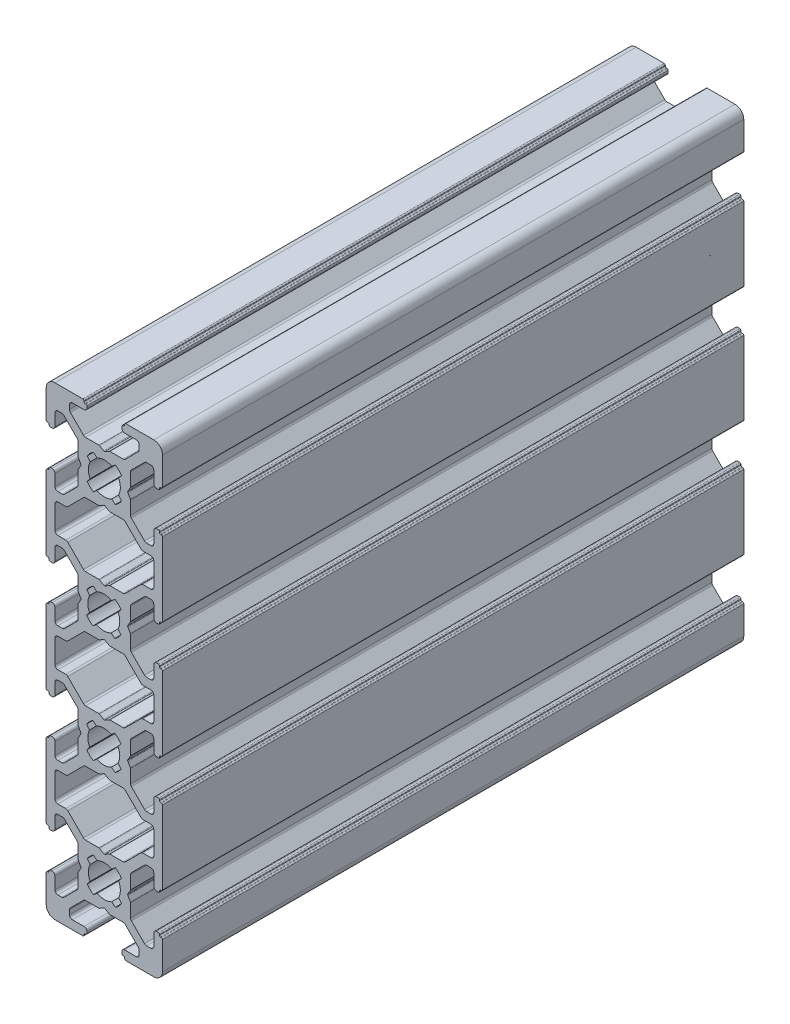
SolidWorks part; units mm, degrees
material "6063-T6"
ref_plane "Спереди" through (0, 0, 0) normal (0, 0, 1) x (1, 0, 0)
ref_plane "Сверху" through (0, 0, 0) normal (0, 1, 0) x (1, 0, 0)
ref_plane "Справа" through (0, 0, 0) normal (1, 0, 0) x (0, 0, -1)
sketch "Эскиз1" plane through (0, 0, 0) normal (0, 0, 1) x (1, 0, 0)
  line L1 (-6.6464, 7.5) -> (-8, 7.5)
  line L2 (3.586, 15.3534) -> (6.2929, 12.6465)
  line L3 (2.4453, -1.2582) -> (2.9477, -1.8871)
  line L4 (4.5, -3.2322) -> (4.5, -0.9536)
  line L5 (-8.5, 3.5) -> (-8.5, 5.45)
  line L6 (0.8538, 15.5267) -> (0.1, 15.9619)
  line L7 (-4.6464, 3.5858) -> (-6.8642, 5.8036)
  line L8 (-3.2322, 4.5) -> (-0.9536, 4.5)
  line L9 (-1.2582, 2.4453) -> (-1.8871, 2.9477)
  line L10 (-3, -9) -> (-3, -9.3)
  line L11 (-10, -3.7) -> (-10, -8.5)
  line L12 (4.4732, 19.1464) -> (4.0381, 19.9)
  line L13 (3.2322, 4.5) -> (0.9536, 4.5)
  line L14 (8.5, 3.5) -> (8.5, 5.5)
  line L15 (8.5, 12) -> (8.5, 8)
  line L18 (3.2323, -4.5) -> (0.9537, -4.5)
  line L19 (-4.4732, 0.8536) -> (-4.0381, 0.1)
  line L20 (-1.2582, -2.4453) -> (-1.8871, -2.9477)
  line L21 (-3.5, -9.7) -> (-3.5, -9.8)
  line L22 (10, 3.7) -> (10, 10)
  line L23 (-9.5, 3.2) -> (-9.5, 3.3)
  line L24 (4.6464, 16.4142) -> (6.9142, 14.1464)
  line L25 (6, -7.2678) -> (6, -8)
  line L32 (-1.3582, 37.5547) -> (-1.9871, 37.0523)
  line L33 (-2.5453, 38.7418) -> (-3.0477, 38.1129)
  line L34 (1.1582, 37.5547) -> (1.7871, 37.0523)
  line L35 (-9.7, 36.5) -> (-9.8, 36.5)
  line L36 (-9.5, 36.8) -> (-9.5, 36.7)
  line L37 (-9, 37) -> (-9.3, 37)
  line L38 (-8.5, 36.5) -> (-8.5, 34.55)
  line L39 (-10, 36.3) -> (-10, 23.7)
  line L40 (10, 36.3) -> (10, 23.7)
  line L41 (8.5, 36.5) -> (8.5, 34.5)
  line L42 (9.5, 36.8) -> (9.5, 36.7)
  line L43 (9.7, 36.5) -> (9.8, 36.5)
  line L44 (9, 37) -> (9.3, 37)
  line L45 (2.3453, 38.7418) -> (2.8477, 38.1129)
  line L54 (4.4732, 0.8536) -> (4.0381, 0.1)
  line L55 (-3.2, -9.5) -> (-3.3, -9.5)
  line L56 (10, -3.7) -> (10, -8.5)
  line L63 (-9, 17.05) -> (-9.3, 17.05)
  line L64 (9.7, 16.55) -> (9.8, 16.55)
  line L65 (6.6464, 12.5) -> (8, 12.5)
  line L66 (-4.5, 16.7678) -> (-4.5, 19.0464)
  line L67 (4.6464, 3.5858) -> (6.9142, 5.8536)
  line L70 (4.4732, 39.1464) -> (4.0381, 39.9)
  line L71 (4.5, 36.7678) -> (4.5, 39.0464)
  line L73 (7.2678, 34) -> (8, 34)
  line L75 (4.6464, 36.4142) -> (6.9142, 34.1464)
  line L76 (3.2322, 35.5) -> (0.9536, 35.5)
  line L77 (0.8536, 35.5268) -> (0.1, 35.9619)
  line L78 (-0.8536, 35.5268) -> (-0.1, 35.9619)
  line L79 (-3.2322, 35.5) -> (-0.9536, 35.5)
  line L80 (3.5858, 35.3535) -> (6.2929, 32.6464)
  line L81 (-3.5858, 35.3535) -> (-6.2929, 32.6464)
  line L82 (-4.5, 36.7678) -> (-4.5, 39.0464)
  line L83 (-4.4732, 39.1464) -> (-4.0381, 39.9)
  line L86 (-7.2178, 34.05) -> (-8, 34.05)
  line L87 (-2.4453, -1.2582) -> (-2.9477, -1.8871)
  line L88 (-4.6464, 36.4142) -> (-6.8642, 34.1964)
  line L89 (-3.7, -10) -> (-8.5, -10)
  line L94 (-9.7, 16.55) -> (-9.8, 16.55)
  line L95 (-7.2678, 14) -> (-8, 14)
  line L96 (-7.3178, -6.05) -> (-8, -6.05)
  line L97 (7.2678, -6) -> (8, -6)
  line L98 (3.5, -9.7) -> (3.5, -9.8)
  line L99 (9.7, 3.5) -> (9.8, 3.5)
  line L100 (-9, -3) -> (-9.3, -3)
  line L101 (-1.2981, 17.5247) -> (-1.9145, 17.0071)
  line L102 (-0.8538, 15.5267) -> (-0.1, 15.9619)
  line L103 (-4.4732, -0.8536) -> (-4.0381, -0.1)
  line L104 (3.5, -8.5) -> (5.5, -8.5)
  line L105 (-10, 16.35) -> (-10, 10)
  line L106 (4.5, 16.7678) -> (4.5, 19.0464)
  line L107 (-3.2323, -4.5) -> (-0.9537, -4.5)
  line L108 (-6, -7.2678) -> (-6, -8)
  line L109 (1.2582, -2.4453) -> (1.8871, -2.9477)
  line L112 (3.5859, -4.6465) -> (5.8536, -6.9142)
  line L113 (-2.4453, 1.2582) -> (-2.9477, 1.8871)
  line L120 (-3.5, -8.5) -> (-5.5, -8.5)
  line L121 (-3.586, 15.3534) -> (-6.2929, 12.6465)
  line L122 (-4.5, 3.2322) -> (-4.5, 0.9536)
  line L123 (9.5, -3.2) -> (9.5, -3.3)
  line L124 (-9, 3) -> (-9.3, 3)
  line L125 (-9.5, -3.2) -> (-9.5, -3.3)
  line L126 (-8.5, 12) -> (-8.5, 8)
  line L127 (-0.8537, -4.4733) -> (-0.1, -4.0381)
  line L128 (0.8536, 4.4732) -> (0.1, 4.0381)
  line L129 (4.6464, -3.5858) -> (6.9142, -5.8536)
  line L130 (3.2, -9.5) -> (3.3, -9.5)
  line L131 (-8.5, -3.5) -> (-8.5, -5.55)
  line L132 (1.2158, 17.5852) -> (1.8564, 17.0978)
  line L133 (-3.5859, -4.6465) -> (-5.8536, -6.9142)
  line L134 (-7.2178, 5.95) -> (-8, 5.95)
  line L135 (1.2582, 2.4453) -> (1.8871, 2.9477)
  line L136 (6.6464, 32.5) -> (8, 32.5)
  line L137 (8.5, 28) -> (8.5, 32)
  line L140 (-8.5, 28) -> (-8.5, 32)
  line L141 (-6.6464, 32.5) -> (-8, 32.5)
  line L142 (-10, 3.7) -> (-10, 10)
  line L143 (-8.5, 16.55) -> (-8.5, 14.5)
  line L144 (-2.5251, 18.7034) -> (-3.0176, 18.0667)
  line L145 (-3.2324, 15.4999) -> (-0.9538, 15.4999)
  line L146 (3.5858, 4.6465) -> (6.2929, 7.3536)
  line L147 (-9.7, 63.5) -> (-9.8, 63.5)
  line L148 (9, 57) -> (9.3, 57)
  line L149 (8.5, 63.5) -> (8.5, 65.5)
  line L150 (-4.5, 63.2322) -> (-4.5, 60.9536)
  line L151 (0.8537, 64.4733) -> (0.1, 64.0381)
  line L152 (-4.6464, 43.5858) -> (-6.9142, 45.8536)
  line L153 (2.3639, 41.2213) -> (2.8758, 41.8425)
  line L154 (-6.6464, 47.5) -> (-8, 47.5)
  line L155 (8.5, 43.45) -> (8.5, 45.5)
  line L156 (4.4732, -0.8536) -> (4.0381, -0.1)
  line L157 (9.5, 56.8) -> (9.5, 56.7)
  line L158 (3, 69) -> (3, 69.3)
  line L159 (4.5, 56.7678) -> (4.5, 59.0464)
  line L160 (7.2678, 54) -> (8, 54)
  line L161 (9.7, -3.5) -> (9.8, -3.5)
  line L162 (-4.4732, 40.8536) -> (-4.0381, 40.1)
  line L163 (-9.5, 16.85) -> (-9.5, 16.75)
  line L164 (6.6464, 52.5) -> (8, 52.5)
  line L165 (9, 42.95) -> (9.3, 42.95)
  line L166 (9.5, 16.85) -> (9.5, 16.75)
  line L167 (7.2678, 14) -> (8, 14)
  line L168 (2.4453, 58.7418) -> (2.9477, 58.1129)
  line L169 (-3.5858, 55.3535) -> (-6.2929, 52.6464)
  line L170 (3.2324, 15.4999) -> (0.9538, 15.4999)
  line L171 (-4.6464, -3.5858) -> (-6.9642, -5.9036)
  line L172 (-0.8536, 4.4732) -> (-0.1, 4.0381)
  line L173 (3.7, -10) -> (8.5, -10)
  line L174 (10, 43.65) -> (10, 50)
  line L175 (-9.7, 56.5) -> (-9.8, 56.5)
  line L176 (9, 63) -> (9.3, 63)
  line L177 (3.7, 70) -> (8.5, 70)
  line L178 (-0.8536, 55.5268) -> (-0.1, 55.9619)
  line L179 (-4.6464, 63.5858) -> (-6.9642, 65.9036)
  line L180 (9, -3) -> (9.3, -3)
  line L181 (-9.7, 3.5) -> (-9.8, 3.5)
  line L182 (3.2324, 44.5001) -> (0.9538, 44.5001)
  line L183 (7.2678, 46) -> (8, 46)
  line L184 (9.5, 43.15) -> (9.5, 43.25)
  line L185 (-9.5, 43.15) -> (-9.5, 43.25)
  line L186 (10, 16.35) -> (10, 10)
  line L187 (9.7, 63.5) -> (9.8, 63.5)
  line L188 (4.4732, 60.8536) -> (4.0381, 60.1)
  line L189 (3.5858, 55.3535) -> (6.2929, 52.6464)
  line L190 (-3.2324, 44.5001) -> (-0.9538, 44.5001)
  line L191 (-2.5251, 41.2966) -> (-3.0176, 41.9333)
  line L192 (-8.5, 43.45) -> (-8.5, 45.5)
  line L193 (-10, 56.3) -> (-10, 50)
  line L194 (1.2582, 57.5547) -> (1.8871, 57.0523)
  line L195 (-7.2178, 54.05) -> (-8, 54.05)
  line L196 (-3.5859, 64.6465) -> (-5.8536, 66.9142)
  line L197 (-3.5858, 4.6465) -> (-6.2929, 7.3536)
  line L198 (2.4453, 1.2582) -> (2.9477, 1.8871)
  line L199 (1.2158, 42.4148) -> (1.8564, 42.9022)
  line L200 (9, 17.05) -> (9.3, 17.05)
  line L201 (-8.5, 63.5) -> (-8.5, 65.55)
  line L202 (3.2, 69.5) -> (3.3, 69.5)
  line L203 (4.6464, 63.5858) -> (6.9142, 65.8536)
  line L204 (0.8536, 55.5268) -> (0.1, 55.9619)
  line L205 (-0.8537, 64.4733) -> (-0.1, 64.0381)
  line L206 (6.6464, 7.5) -> (8, 7.5)
  line L208 (-8.5, 48) -> (-8.5, 52)
  line L209 (-4.4732, 19.1464) -> (-4.0381, 19.9)
  line L210 (-9.5, 63.2) -> (-9.5, 63.3)
  line L211 (-9, 57) -> (-9.3, 57)
  line L212 (9.5, 63.2) -> (9.5, 63.3)
  line L213 (-4.5, 56.7678) -> (-4.5, 59.0464)
  line L214 (-3.586, 44.6466) -> (-6.2929, 47.3535)
  line L215 (7.2678, 6) -> (8, 6)
  line L216 (4.5, 3.2322) -> (4.5, 0.9536)
  line L217 (3, -9) -> (3, -9.3)
  line L218 (9.5, 3.2) -> (9.5, 3.3)
  line L219 (8.5, 16.55) -> (8.5, 14.5)
  line L220 (-3.5, 68.5) -> (-5.5, 68.5)
  line L221 (-2.4453, 58.7418) -> (-2.9477, 58.1129)
  line L222 (3.5859, 64.6465) -> (5.8536, 66.9142)
  line L223 (1.2582, 62.4453) -> (1.8871, 62.9477)
  line L224 (-6, 67.2678) -> (-6, 68)
  line L225 (-3.2323, 64.5) -> (-0.9537, 64.5)
  line L226 (-6.6464, 12.5) -> (-8, 12.5)
  line L227 (4.5, 43.2322) -> (4.5, 40.9536)
  line L228 (2.3639, 18.7787) -> (2.8758, 18.1575)
  line L229 (-10, 43.65) -> (-10, 50)
  line L230 (-4.6464, 16.4142) -> (-6.9142, 14.1464)
  line L231 (3.5, 68.5) -> (5.5, 68.5)
  line L232 (-4.4732, 60.8536) -> (-4.0381, 60.1)
  line L233 (-0.8538, 44.4733) -> (-0.1, 44.0381)
  line L234 (-1.2981, 42.4753) -> (-1.9145, 42.9929)
  line L235 (0.8537, -4.4733) -> (0.1, -4.0381)
  line L236 (-9, 63) -> (-9.3, 63)
  line L237 (9.7, 56.5) -> (9.8, 56.5)
  line L238 (3.5, 69.7) -> (3.5, 69.8)
  line L239 (7.2678, 66) -> (8, 66)
  line L240 (-7.3178, 66.05) -> (-8, 66.05)
  line L241 (-4.5, -3.2322) -> (-4.5, -0.9536)
  line L242 (-7.2678, 46) -> (-8, 46)
  line L243 (8.5, -3.5) -> (8.5, -5.5)
  line L244 (-9.7, 43.45) -> (-9.8, 43.45)
  line L245 (9, 3) -> (9.3, 3)
  line L246 (-3.7, 70) -> (-8.5, 70)
  line L247 (-2.4453, 61.2582) -> (-2.9477, 61.8871)
  line L248 (4.6464, 56.4142) -> (6.9142, 54.1464)
  line L249 (-4.5, 43.2322) -> (-4.5, 40.9536)
  line L250 (6.6464, 47.5) -> (8, 47.5)
  line L251 (9.7, 43.45) -> (9.8, 43.45)
  line L252 (-9, 42.95) -> (-9.3, 42.95)
  line L253 (-9.7, -3.5) -> (-9.8, -3.5)
  line L254 (10, 63.7) -> (10, 68.5)
  line L255 (-3.2, 69.5) -> (-3.3, 69.5)
  line L256 (4.4732, 59.1464) -> (4.0381, 59.9)
  line L257 (6, 67.2678) -> (6, 68)
  line L258 (-6.6464, 27.5) -> (-8, 27.5)
  line L259 (4.6464, 43.5858) -> (6.9142, 45.8536)
  line L260 (6.6464, 27.5) -> (8, 27.5)
  line L261 (-4.6464, 23.5858) -> (-6.8642, 25.8036)
  line L262 (-9.5, 56.8) -> (-9.5, 56.7)
  line L263 (10, 56.3) -> (10, 50)
  line L264 (-3.5, 69.7) -> (-3.5, 69.8)
  line L265 (-1.2582, 62.4453) -> (-1.8871, 62.9477)
  line L266 (-4.4732, 59.1464) -> (-4.0381, 59.9)
  line L267 (3.2323, 64.5) -> (0.9537, 64.5)
  line L268 (-7.2178, 25.95) -> (-8, 25.95)
  line L269 (-4.4732, 20.8536) -> (-4.0381, 20.1)
  line L270 (8.5, 48) -> (8.5, 52)
  line L271 (-4.5, 23.2322) -> (-4.5, 20.9536)
  line L272 (-3.5858, 24.6465) -> (-6.2929, 27.3536)
  line L273 (8.5, 56.5) -> (8.5, 54.5)
  line L274 (3.2322, 55.5) -> (0.9536, 55.5)
  line L275 (3.5858, 24.6465) -> (6.2929, 27.3536)
  line L276 (4.4732, 40.8536) -> (4.0381, 40.1)
  line L277 (-10, 63.7) -> (-10, 68.5)
  line L278 (-3, 69) -> (-3, 69.3)
  line L279 (-1.2582, 57.5547) -> (-1.8871, 57.0523)
  line L280 (-3.2322, 55.5) -> (-0.9536, 55.5)
  line L281 (-4.6464, 56.4142) -> (-6.8642, 54.1964)
  line L282 (-3.2322, 24.5) -> (-0.9536, 24.5)
  line L283 (-0.8536, 24.4732) -> (-0.1, 24.0381)
  line L284 (0.8538, 44.4733) -> (0.1, 44.0381)
  line L285 (0.8536, 24.4732) -> (0.1, 24.0381)
  line L286 (3.2322, 24.5) -> (0.9536, 24.5)
  line L287 (-8.5, 56.5) -> (-8.5, 54.55)
  line L288 (4.5, 63.2322) -> (4.5, 60.9536)
  line L289 (2.4453, 61.2582) -> (2.9477, 61.8871)
  line L290 (3.586, 44.6466) -> (6.2929, 47.3535)
  line L291 (-6.6464, 52.5) -> (-8, 52.5)
  line L292 (4.6464, 23.5858) -> (6.9142, 25.8536)
  line L293 (7.2678, 26) -> (8, 26)
  line L294 (4.5, 23.2322) -> (4.5, 20.9536)
  line L295 (4.4732, 20.8536) -> (4.0381, 20.1)
  line L296 (2.3453, 21.2582) -> (2.8477, 21.8871)
  line L297 (9, 23) -> (9.3, 23)
  line L298 (9.7, 23.5) -> (9.8, 23.5)
  line L299 (9.5, 23.2) -> (9.5, 23.3)
  line L300 (8.5, 23.5) -> (8.5, 25.5)
  line L301 (-8.5, 23.5) -> (-8.5, 25.45)
  line L302 (-9, 23) -> (-9.3, 23)
  line L303 (-9.5, 23.2) -> (-9.5, 23.3)
  line L304 (-9.7, 23.5) -> (-9.8, 23.5)
  line L305 (1.1582, 22.4453) -> (1.7871, 22.9477)
  line L306 (-2.5453, 21.2582) -> (-3.0477, 21.8871)
  line L307 (-1.3582, 22.4453) -> (-1.9871, 22.9477)
  arc A0 (4.6464, 16.4142) -> (4.5, 16.7678) centre (5, 16.7678) cw
  arc A1 (-4.5, 19.0464) -> (-4.4732, 19.1464) centre (-4.3, 19.0464) cw
  arc A2 (-4.4732, 0.8536) -> (-4.5, 0.9536) centre (-4.3, 0.9536) cw
  arc A3 (-3.2322, 4.5) -> (-3.5858, 4.6465) centre (-3.2322, 5) cw
  arc A4 (2.9477, -1.8871) -> (1.8871, -2.9477) centre (0, 0) cw
  arc A5 (-1.2582, 2.4453) -> (1.2582, 2.4453) centre (0, 0) cw
  arc A6 (9, 3) -> (8.5, 3.5) centre (9, 3.5) cw
  arc A7 (6.2929, 7.3536) -> (6.6464, 7.5) centre (6.6464, 7) cw
  arc A8 (4.0381, 19.9) -> (4.0113, 20) centre (4.2113, 20) cw
  arc A9 (-4.5, 16.7678) -> (-4.6464, 16.4142) centre (-5, 16.7678) cw
  arc A10 (-0.1, -4.0381) -> (0.1, -4.0381) centre (0, -4.2113) cw
  arc A11 (-0.8537, -4.4733) -> (-0.9537, -4.5) centre (-0.9537, -4.3) cw
  arc A12 (-2.9477, 1.8871) -> (-1.8871, 2.9477) centre (0, 0) cw
  arc A15 (1.8871, 2.9477) -> (2.9477, 1.8871) centre (0, 0) cw
  arc A16 (-9, -3) -> (-8.5, -3.5) centre (-9, -3.5) cw
  arc A17 (6.6464, 12.5) -> (6.2929, 12.6465) centre (6.6464, 13) cw
  arc A18 (3.2324, 15.4999) -> (3.586, 15.3534) centre (3.2324, 14.9999) cw
  arc A19 (-6, -7.2678) -> (-5.8536, -6.9142) centre (-5.5, -7.2678) cw
  arc A20 (-4.5, -0.9536) -> (-4.4732, -0.8536) centre (-4.3, -0.9536) cw
  arc A21 (-3.5, -9.7) -> (-3.3, -9.5) centre (-3.3, -9.7) cw
  arc A22 (-9.5, -3.2) -> (-9.3, -3) centre (-9.3, -3.2) cw
  arc A24 (-1.9871, 37.0523) -> (-3.0477, 38.1129) centre (-0.1, 40) cw
  arc A25 (1.1582, 37.5547) -> (-1.3582, 37.5547) centre (-0.1, 40) cw
  arc A26 (2.8477, 38.1129) -> (1.7871, 37.0523) centre (-0.1, 40) cw
  arc A28 (-9.7, 36.5) -> (-9.5, 36.7) centre (-9.7, 36.7) ccw
  arc A29 (-9.8, 36.5) -> (-10, 36.3) centre (-9.8, 36.3) ccw
  arc A30 (-9.3, 37) -> (-9.5, 36.8) centre (-9.3, 36.8) ccw
  arc A31 (-8.5, 36.5) -> (-9, 37) centre (-9, 36.5) ccw
  arc A32 (9.5, 36.8) -> (9.3, 37) centre (9.3, 36.8) ccw
  arc A33 (10, 36.3) -> (9.8, 36.5) centre (9.8, 36.3) ccw
  arc A34 (9.5, 36.7) -> (9.7, 36.5) centre (9.7, 36.7) ccw
  arc A35 (9, 37) -> (8.5, 36.5) centre (9, 36.5) ccw
  arc A49 (2.3453, 21.2582) -> (2.3639, 18.7787) centre (-0.1, 20) cw
  arc A51 (-0.1, 15.9619) -> (0.1, 15.9619) centre (0, 15.7887) cw
  arc A55 (4.0113, 40) -> (4.0381, 39.9) centre (4.2113, 40) ccw
  arc A56 (4.5, 39.0464) -> (4.4732, 39.1464) centre (4.3, 39.0464) ccw
  arc A58 (6.9142, 34.1464) -> (7.2678, 34) centre (7.2678, 34.5) ccw
  arc A59 (4.5, 36.7678) -> (4.6464, 36.4142) centre (5, 36.7678) ccw
  arc A61 (0.9537, -4.5) -> (0.8537, -4.4733) centre (0.9537, -4.3) cw
  arc A62 (0.1, 35.9619) -> (-0.1, 35.9619) centre (0, 35.7887) ccw
  arc A63 (-0.9536, 35.5) -> (-0.8536, 35.5268) centre (-0.9536, 35.7) ccw
  arc A64 (0.8536, 35.5268) -> (0.9536, 35.5) centre (0.9536, 35.7) ccw
  arc A65 (-3.2322, 35.5) -> (-3.5858, 35.3535) centre (-3.2322, 35) ccw
  arc A66 (3.5858, 35.3535) -> (3.2322, 35.5) centre (3.2322, 35) ccw
  arc A67 (-4.0381, 39.9) -> (-4.0113, 40) centre (-4.2113, 40) ccw
  arc A68 (3.5858, 4.6465) -> (3.2322, 4.5) centre (3.2322, 5) cw
  arc A69 (-4.4732, 39.1464) -> (-4.5, 39.0464) centre (-4.3, 39.0464) ccw
  arc A70 (3.7, -10) -> (3.5, -9.8) centre (3.7, -9.8) cw
  arc A71 (-3, -9.3) -> (-3.2, -9.5) centre (-3.2, -9.3) cw
  arc A72 (-4.6464, 36.4142) -> (-4.5, 36.7678) centre (-5, 36.7678) ccw
  arc A73 (-7.2178, 34.05) -> (-6.8642, 34.1964) centre (-7.2178, 34.55) ccw
  arc A74 (-9.8, 3.5) -> (-10, 3.7) centre (-9.8, 3.7) cw
  arc A75 (9.3, 17.05) -> (9.5, 16.85) centre (9.3, 16.85) cw
  arc A76 (7.2678, 14) -> (6.9142, 14.1464) centre (7.2678, 14.5) cw
  arc A77 (0.9538, 15.4999) -> (0.8538, 15.5267) centre (0.9538, 15.6999) cw
  arc A80 (8, 34) -> (8.5, 34.5) centre (8, 34.5) ccw
  arc A81 (-8.5, 34.55) -> (-8, 34.05) centre (-8, 34.55) ccw
  arc A85 (-3.586, 15.3534) -> (-3.2324, 15.4999) centre (-3.2324, 14.9999) cw
  arc A86 (-5.5, -8.5) -> (-6, -8) centre (-5.5, -8) cw
  arc A89 (-0.9536, 4.5) -> (-0.8536, 4.4732) centre (-0.9536, 4.3) cw
  arc A90 (-3.5, -9.8) -> (-3.7, -10) centre (-3.7, -9.8) cw
  arc A92 (9.8, 16.55) -> (10, 16.35) centre (9.8, 16.35) cw
  arc A93 (6, -8) -> (5.5, -8.5) centre (5.5, -8) cw
  arc A94 (0.1, 4.0381) -> (-0.1, 4.0381) centre (0, 4.2113) cw
  arc A95 (-1.8871, -2.9477) -> (-2.9477, -1.8871) centre (0, 0) cw
  arc A96 (-3.5, -8.5) -> (-3, -9) centre (-3.5, -9) cw
  arc A97 (9.7, 16.55) -> (9.5, 16.75) centre (9.7, 16.75) cw
  arc A98 (-8, 7.5) -> (-8.5, 8) centre (-8, 8) cw
  arc A99 (1.2158, 17.5852) -> (-1.2981, 17.5247) centre (-0.1, 20) cw
  arc A100 (-8, -6.05) -> (-8.5, -5.55) centre (-8, -5.55) cw
  arc A101 (-6.9642, -5.9036) -> (-7.3178, -6.05) centre (-7.3178, -5.55) cw
  arc A102 (9.3, -3) -> (9.5, -3.2) centre (9.3, -3.2) cw
  arc A106 (9.5, 3.2) -> (9.3, 3) centre (9.3, 3.2) cw
  arc A107 (-10, 16.35) -> (-9.8, 16.55) centre (-9.8, 16.35) cw
  arc A108 (-6.2929, 12.6465) -> (-6.6464, 12.5) centre (-6.6464, 13) cw
  arc A109 (-4.0113, 20) -> (-4.0381, 19.9) centre (-4.2113, 20) cw
  arc A110 (10, -8.5) -> (8.5, -10) centre (8.5, -8.5) cw
  arc A111 (-4.6464, 3.5858) -> (-4.5, 3.2322) centre (-5, 3.2322) cw
  arc A112 (8.5, -3.5) -> (9, -3) centre (9, -3.5) cw
  arc A118 (-8.5, 12) -> (-8, 12.5) centre (-8, 12) cw
  arc A119 (-6.9142, 14.1464) -> (-7.2678, 14) centre (-7.2678, 14.5) cw
  arc A120 (-8.5, -10) -> (-10, -8.5) centre (-8.5, -8.5) cw
  arc A121 (2.4453, 1.2582) -> (2.4453, -1.2582) centre (0, 0) cw
  arc A122 (9.8, -3.5) -> (10, -3.7) centre (9.8, -3.7) cw
  arc A123 (-9.7, 3.5) -> (-9.5, 3.3) centre (-9.7, 3.3) cw
  arc A124 (8.5, 14.5) -> (8, 14) centre (8, 14.5) cw
  arc A125 (8, 6) -> (8.5, 5.5) centre (8, 5.5) cw
  arc A126 (-3.5859, -4.6465) -> (-3.2323, -4.5) centre (-3.2323, -5) cw
  arc A127 (4.0381, -0.1) -> (4.0381, 0.1) centre (4.2113, 0) cw
  arc A128 (-10, -3.7) -> (-9.8, -3.5) centre (-9.8, -3.7) cw
  arc A129 (-6.6464, 7.5) -> (-6.2929, 7.3536) centre (-6.6464, 7) cw
  arc A130 (4.4732, 19.1464) -> (4.5, 19.0464) centre (4.3, 19.0464) cw
  arc A131 (-4.0381, 0.1) -> (-4.0381, -0.1) centre (-4.2113, 0) cw
  arc A132 (-6.6464, 32.5) -> (-6.2929, 32.6464) centre (-6.6464, 33) ccw
  arc A133 (-8, 32.5) -> (-8.5, 32) centre (-8, 32) ccw
  arc A136 (6.2929, 32.6464) -> (6.6464, 32.5) centre (6.6464, 33) ccw
  arc A137 (8.5, 32) -> (8, 32.5) centre (8, 32) ccw
  arc A140 (4.6464, -3.5858) -> (4.5, -3.2322) centre (5, -3.2322) cw
  arc A141 (-9.3, 57) -> (-9.5, 56.8) centre (-9.3, 56.8) ccw
  arc A142 (4.5, 59.0464) -> (4.4732, 59.1464) centre (4.3, 59.0464) ccw
  arc A143 (0.8536, 55.5268) -> (0.9536, 55.5) centre (0.9536, 55.7) ccw
  arc A144 (5.8536, 66.9142) -> (6, 67.2678) centre (5.5, 67.2678) ccw
  arc A145 (6.9142, 5.8536) -> (7.2678, 6) centre (7.2678, 5.5) cw
  arc A146 (-0.8538, 44.4733) -> (-0.9538, 44.5001) centre (-0.9538, 44.3001) ccw
  arc A147 (3, -9) -> (3.5, -8.5) centre (3.5, -9) cw
  arc A148 (-9.5, 43.25) -> (-9.7, 43.45) centre (-9.7, 43.25) ccw
  arc A149 (-2.5251, 18.7034) -> (-2.5453, 21.2582) centre (-0.1, 20) cw
  arc A150 (-2.4453, 61.2582) -> (-2.4453, 58.7418) centre (0, 60) ccw
  arc A151 (4.4732, 60.8536) -> (4.5, 60.9536) centre (4.3, 60.9536) ccw
  arc A152 (4.5, 56.7678) -> (4.6464, 56.4142) centre (5, 56.7678) ccw
  arc A153 (-7.2178, 54.05) -> (-6.8642, 54.1964) centre (-7.2178, 54.55) ccw
  arc A154 (-8, 14) -> (-8.5, 14.5) centre (-8, 14.5) cw
  arc A155 (-8.5, 5.45) -> (-8, 5.95) centre (-8, 5.45) cw
  arc A156 (-4.5, -3.2322) -> (-4.6464, -3.5858) centre (-5, -3.2322) cw
  arc A157 (8.5, 52) -> (8, 52.5) centre (8, 52) ccw
  arc A158 (10, 3.7) -> (9.8, 3.5) centre (9.8, 3.7) cw
  arc A159 (-9.5, 43.15) -> (-9.3, 42.95) centre (-9.3, 43.15) ccw
  arc A160 (-9, 42.95) -> (-8.5, 43.45) centre (-9, 43.45) ccw
  arc A161 (3.3, 69.5) -> (3.5, 69.7) centre (3.3, 69.7) ccw
  arc A162 (3.2323, 64.5) -> (3.5859, 64.6465) centre (3.2323, 65) ccw
  arc A163 (-8.5, 3.5) -> (-9, 3) centre (-9, 3.5) cw
  arc A164 (-9.5, -3.3) -> (-9.7, -3.5) centre (-9.7, -3.3) cw
  arc A165 (2.8758, 18.1575) -> (1.8564, 17.0978) centre (-0.1, 20) cw
  arc A166 (8.5, -5.5) -> (8, -6) centre (8, -5.5) cw
  arc A167 (9.7, 63.5) -> (9.5, 63.3) centre (9.7, 63.3) ccw
  arc A168 (3.2, 69.5) -> (3, 69.3) centre (3.2, 69.3) ccw
  arc A169 (1.2582, 62.4453) -> (-1.2582, 62.4453) centre (0, 60) ccw
  arc A170 (7.2678, -6) -> (6.9142, -5.8536) centre (7.2678, -5.5) cw
  arc A171 (9.5, 3.3) -> (9.7, 3.5) centre (9.7, 3.3) cw
  arc A172 (-1.9145, 42.9929) -> (-3.0176, 41.9333) centre (-0.1, 40) ccw
  arc A173 (8, 47.5) -> (8.5, 48) centre (8, 48) ccw
  arc A174 (8.5, 43.45) -> (9, 42.95) centre (9, 43.45) ccw
  arc A175 (8.5, 16.55) -> (9, 17.05) centre (9, 16.55) cw
  arc A176 (9.5, 56.7) -> (9.7, 56.5) centre (9.7, 56.7) ccw
  arc A177 (7.2678, 66) -> (6.9142, 65.8536) centre (7.2678, 65.5) ccw
  arc A178 (8.5, 65.5) -> (8, 66) centre (8, 65.5) ccw
  arc A179 (8, 12.5) -> (8.5, 12) centre (8, 12) cw
  arc A180 (-1.9145, 17.0071) -> (-3.0176, 18.0667) centre (-0.1, 20) cw
  arc A181 (2.8758, 41.8425) -> (1.8564, 42.9022) centre (-0.1, 40) ccw
  arc A182 (-9.5, 63.3) -> (-9.7, 63.5) centre (-9.7, 63.3) ccw
  arc A183 (-8.5, 56.5) -> (-9, 57) centre (-9, 56.5) ccw
  arc A184 (10, 56.3) -> (9.8, 56.5) centre (9.8, 56.3) ccw
  arc A185 (-4.5, 63.2322) -> (-4.6464, 63.5858) centre (-5, 63.2322) ccw
  arc A186 (-8.5, 54.55) -> (-8, 54.05) centre (-8, 54.55) ccw
  arc A187 (-8, 46) -> (-8.5, 45.5) centre (-8, 45.5) ccw
  arc A188 (1.2582, -2.4453) -> (-1.2582, -2.4453) centre (0, 0) cw
  arc A189 (-2.5251, 41.2966) -> (-2.5453, 38.7418) centre (-0.1, 40) ccw
  arc A190 (3.2, -9.5) -> (3, -9.3) centre (3.2, -9.3) cw
  arc A191 (9.7, -3.5) -> (9.5, -3.3) centre (9.7, -3.3) cw
  arc A192 (3, 69) -> (3.5, 68.5) centre (3.5, 69) ccw
  arc A193 (6.9142, 54.1464) -> (7.2678, 54) centre (7.2678, 54.5) ccw
  arc A194 (4.6464, 63.5858) -> (4.5, 63.2322) centre (5, 63.2322) ccw
  arc A195 (-4.0381, 59.9) -> (-4.0381, 60.1) centre (-4.2113, 60) ccw
  arc A196 (3.2323, -4.5) -> (3.5859, -4.6465) centre (3.2323, -5) cw
  arc A197 (3.3, -9.5) -> (3.5, -9.7) centre (3.3, -9.7) cw
  arc A198 (4.4732, 40.8536) -> (4.5, 40.9536) centre (4.3, 40.9536) ccw
  arc A199 (-6.6464, 52.5) -> (-6.2929, 52.6464) centre (-6.6464, 53) ccw
  arc A200 (-9, 17.05) -> (-8.5, 16.55) centre (-9, 16.55) cw
  arc A201 (-10, 63.7) -> (-9.8, 63.5) centre (-9.8, 63.7) ccw
  arc A202 (4.0381, 60.1) -> (4.0381, 59.9) centre (4.2113, 60) ccw
  arc A203 (-3.5859, 64.6465) -> (-3.2323, 64.5) centre (-3.2323, 65) ccw
  arc A204 (8, 54) -> (8.5, 54.5) centre (8, 54.5) ccw
  arc A205 (8.5, 45.5) -> (8, 46) centre (8, 45.5) ccw
  arc A206 (-9.7, 56.5) -> (-9.5, 56.7) centre (-9.7, 56.7) ccw
  arc A207 (9.8, 63.5) -> (10, 63.7) centre (9.8, 63.7) ccw
  arc A208 (2.4453, 58.7418) -> (2.4453, 61.2582) centre (0, 60) ccw
  arc A209 (-8.5, 70) -> (-10, 68.5) centre (-8.5, 68.5) ccw
  arc A211 (-6.9142, 45.8536) -> (-7.2678, 46) centre (-7.2678, 45.5) ccw
  arc A212 (-8.5, 48) -> (-8, 47.5) centre (-8, 48) ccw
  arc A214 (-9.5, 16.85) -> (-9.3, 17.05) centre (-9.3, 16.85) cw
  arc A215 (8.5, 63.5) -> (9, 63) centre (9, 63.5) ccw
  arc A216 (-4.6464, 56.4142) -> (-4.5, 56.7678) centre (-5, 56.7678) ccw
  arc A217 (10, 68.5) -> (8.5, 70) centre (8.5, 68.5) ccw
  arc A218 (-4.0113, 40) -> (-4.0381, 40.1) centre (-4.2113, 40) ccw
  arc A219 (-6.2929, 47.3535) -> (-6.6464, 47.5) centre (-6.6464, 47) ccw
  arc A220 (8.5, 8) -> (8, 7.5) centre (8, 8) cw
  arc A221 (-10, 43.65) -> (-9.8, 43.45) centre (-9.8, 43.65) ccw
  arc A222 (9.5, 56.8) -> (9.3, 57) centre (9.3, 56.8) ccw
  arc A223 (9.3, 63) -> (9.5, 63.2) centre (9.3, 63.2) ccw
  arc A224 (-6.9642, 65.9036) -> (-7.3178, 66.05) centre (-7.3178, 65.55) ccw
  arc A225 (-8, 66.05) -> (-8.5, 65.55) centre (-8, 65.55) ccw
  arc A226 (-7.2178, 5.95) -> (-6.8642, 5.8036) centre (-7.2178, 5.45) cw
  arc A227 (1.2158, 42.4148) -> (-1.2981, 42.4753) centre (-0.1, 40) ccw
  arc A228 (-8, 52.5) -> (-8.5, 52) centre (-8, 52) ccw
  arc A229 (9.7, 43.45) -> (9.5, 43.25) centre (9.7, 43.25) ccw
  arc A230 (4.5, 3.2322) -> (4.6464, 3.5858) centre (5, 3.2322) cw
  arc A231 (-3.5, 68.5) -> (-3, 69) centre (-3.5, 69) ccw
  arc A232 (-1.8871, 62.9477) -> (-2.9477, 61.8871) centre (0, 60) ccw
  arc A233 (0.1, 55.9619) -> (-0.1, 55.9619) centre (0, 55.7887) ccw
  arc A234 (6, 68) -> (5.5, 68.5) centre (5.5, 68) ccw
  arc A235 (4.4732, -0.8536) -> (4.5, -0.9536) centre (4.3, -0.9536) cw
  arc A236 (-2.4453, -1.2582) -> (-2.4453, 1.2582) centre (0, 0) cw
  arc A237 (-9.5, 16.75) -> (-9.7, 16.55) centre (-9.7, 16.75) cw
  arc A238 (9.8, 43.45) -> (10, 43.65) centre (9.8, 43.65) ccw
  arc A239 (-0.8538, 15.5267) -> (-0.9538, 15.4999) centre (-0.9538, 15.6999) cw
  arc A240 (-3.5, 69.8) -> (-3.7, 70) centre (-3.7, 69.8) ccw
  arc A241 (-0.9536, 55.5) -> (-0.8536, 55.5268) centre (-0.9536, 55.7) ccw
  arc A242 (-5.5, 68.5) -> (-6, 68) centre (-5.5, 68) ccw
  arc A243 (-3.586, 44.6466) -> (-3.2324, 44.5001) centre (-3.2324, 45.0001) ccw
  arc A244 (0.9538, 44.5001) -> (0.8538, 44.4733) centre (0.9538, 44.3001) ccw
  arc A245 (7.2678, 46) -> (6.9142, 45.8536) centre (7.2678, 45.5) ccw
  arc A246 (9.3, 42.95) -> (9.5, 43.15) centre (9.3, 43.15) ccw
  arc A247 (-9.8, 56.5) -> (-10, 56.3) centre (-9.8, 56.3) ccw
  arc A248 (-3, 69.3) -> (-3.2, 69.5) centre (-3.2, 69.3) ccw
  arc A249 (3.7, 70) -> (3.5, 69.8) centre (3.7, 69.8) ccw
  arc A250 (3.5858, 55.3535) -> (3.2322, 55.5) centre (3.2322, 55) ccw
  arc A251 (0.9537, 64.5) -> (0.8537, 64.4733) centre (0.9537, 64.3) ccw
  arc A252 (5.8536, -6.9142) -> (6, -7.2678) centre (5.5, -7.2678) cw
  arc A253 (-0.1, 44.0381) -> (0.1, 44.0381) centre (0, 44.2113) ccw
  arc A254 (2.3453, 38.7418) -> (2.3639, 41.2213) centre (-0.1, 40) ccw
  arc A255 (0.8536, 4.4732) -> (0.9536, 4.5) centre (0.9536, 4.3) cw
  arc A256 (-9.5, 63.2) -> (-9.3, 63) centre (-9.3, 63.2) ccw
  arc A257 (-3.5, 69.7) -> (-3.3, 69.5) centre (-3.3, 69.7) ccw
  arc A258 (-4.5, 60.9536) -> (-4.4732, 60.8536) centre (-4.3, 60.9536) ccw
  arc A259 (-6, 67.2678) -> (-5.8536, 66.9142) centre (-5.5, 67.2678) ccw
  arc A260 (3.2324, 44.5001) -> (3.586, 44.6466) centre (3.2324, 45.0001) ccw
  arc A261 (6.6464, 47.5) -> (6.2929, 47.3535) centre (6.6464, 47) ccw
  arc A262 (4.5, 0.9536) -> (4.4732, 0.8536) centre (4.3, 0.9536) cw
  arc A263 (-9, 63) -> (-8.5, 63.5) centre (-9, 63.5) ccw
  arc A264 (1.8871, 57.0523) -> (2.9477, 58.1129) centre (0, 60) ccw
  arc A265 (-2.9477, 58.1129) -> (-1.8871, 57.0523) centre (0, 60) ccw
  arc A266 (-0.8537, 64.4733) -> (-0.9537, 64.5) centre (-0.9537, 64.3) ccw
  arc A267 (-0.1, 64.0381) -> (0.1, 64.0381) centre (0, 64.2113) ccw
  arc A268 (-4.5, 43.2322) -> (-4.6464, 43.5858) centre (-5, 43.2322) ccw
  arc A269 (4.0381, 40.1) -> (4.0113, 40) centre (4.2113, 40) ccw
  arc A270 (6.2929, 52.6464) -> (6.6464, 52.5) centre (6.6464, 53) ccw
  arc A271 (-9.3, 3) -> (-9.5, 3.2) centre (-9.3, 3.2) cw
  arc A272 (9, 57) -> (8.5, 56.5) centre (9, 56.5) ccw
  arc A273 (-1.2582, 57.5547) -> (1.2582, 57.5547) centre (0, 60) ccw
  arc A274 (2.9477, 61.8871) -> (1.8871, 62.9477) centre (0, 60) ccw
  arc A275 (-3.2322, 55.5) -> (-3.5858, 55.3535) centre (-3.2322, 55) ccw
  arc A276 (-4.4732, 59.1464) -> (-4.5, 59.0464) centre (-4.3, 59.0464) ccw
  arc A277 (8.5, 28) -> (8, 27.5) centre (8, 28) cw
  arc A278 (-4.5, 40.9536) -> (-4.4732, 40.8536) centre (-4.3, 40.9536) ccw
  arc A279 (4.6464, 43.5858) -> (4.5, 43.2322) centre (5, 43.2322) ccw
  arc A280 (6.2929, 27.3536) -> (6.6464, 27.5) centre (6.6464, 27) cw
  arc A281 (-8, 27.5) -> (-8.5, 28) centre (-8, 28) cw
  arc A282 (-6.6464, 27.5) -> (-6.2929, 27.3536) centre (-6.6464, 27) cw
  arc A283 (-8.5, 25.45) -> (-8, 25.95) centre (-8, 25.45) cw
  arc A284 (8, 26) -> (8.5, 25.5) centre (8, 25.5) cw
  arc A285 (-7.2178, 25.95) -> (-6.8642, 25.8036) centre (-7.2178, 25.45) cw
  arc A286 (-4.6464, 23.5858) -> (-4.5, 23.2322) centre (-5, 23.2322) cw
  arc A287 (-4.4732, 20.8536) -> (-4.5, 20.9536) centre (-4.3, 20.9536) cw
  arc A288 (-4.0381, 20.1) -> (-4.0113, 20) centre (-4.2113, 20) cw
  arc A289 (3.5858, 24.6465) -> (3.2322, 24.5) centre (3.2322, 25) cw
  arc A290 (-3.2322, 24.5) -> (-3.5858, 24.6465) centre (-3.2322, 25) cw
  arc A291 (0.8536, 24.4732) -> (0.9536, 24.5) centre (0.9536, 24.3) cw
  arc A292 (-0.9536, 24.5) -> (-0.8536, 24.4732) centre (-0.9536, 24.3) cw
  arc A293 (0.1, 24.0381) -> (-0.1, 24.0381) centre (0, 24.2113) cw
  arc A294 (4.5, 23.2322) -> (4.6464, 23.5858) centre (5, 23.2322) cw
  arc A295 (6.9142, 25.8536) -> (7.2678, 26) centre (7.2678, 25.5) cw
  arc A296 (4.5, 20.9536) -> (4.4732, 20.8536) centre (4.3, 20.9536) cw
  arc A297 (4.0113, 20) -> (4.0381, 20.1) centre (4.2113, 20) cw
  arc A298 (9, 23) -> (8.5, 23.5) centre (9, 23.5) cw
  arc A299 (9.5, 23.3) -> (9.7, 23.5) centre (9.7, 23.3) cw
  arc A300 (10, 23.7) -> (9.8, 23.5) centre (9.8, 23.7) cw
  arc A301 (9.5, 23.2) -> (9.3, 23) centre (9.3, 23.2) cw
  arc A302 (-8.5, 23.5) -> (-9, 23) centre (-9, 23.5) cw
  arc A303 (-9.3, 23) -> (-9.5, 23.2) centre (-9.3, 23.2) cw
  arc A304 (-9.8, 23.5) -> (-10, 23.7) centre (-9.8, 23.7) cw
  arc A305 (-9.7, 23.5) -> (-9.5, 23.3) centre (-9.7, 23.3) cw
  arc A306 (2.8477, 21.8871) -> (1.7871, 22.9477) centre (-0.1, 20) ccw
  arc A307 (1.1582, 22.4453) -> (-1.3582, 22.4453) centre (-0.1, 20) ccw
  arc A308 (-1.9871, 22.9477) -> (-3.0477, 21.8871) centre (-0.1, 20) ccw
  point P2 (-8.5, 30)
  point P4 (8.5, 30)
  point P6 (10, 30)
  dimension "D21" = 6
  dimension "D31" = 12
extrude "Бобышка-Вытянуть1" add sketch "Эскиз1" along normal blind 100
